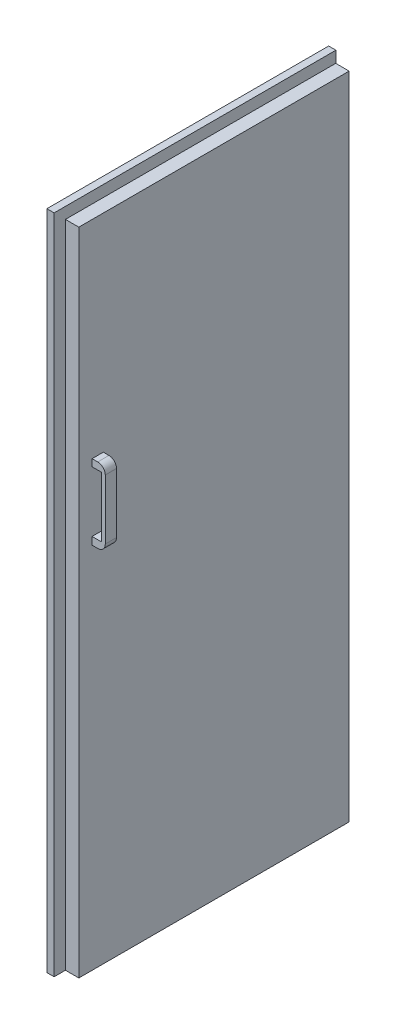
SolidWorks part; units mm, degrees
ref_plane "Front Plane" through (0, 0, 0) normal (0, 0, 1) x (1, 0, 0)
ref_plane "Top Plane" through (0, 0, 0) normal (0, 1, 0) x (1, 0, 0)
ref_plane "Right Plane" through (0, 0, 0) normal (1, 0, 0) x (0, 0, -1)
sketch "Sketch1" plane through (0, 0, 0) normal (0, 1, 0) x (1, 0, 0)
  line L1 (0, 0) -> (54.7584, 0)
  line L2 (0, 0) -> (0, -717)
  line L3 (0, -717) -> (54.7584, -717)
  line L4 (54.7584, 0) -> (54.7584, -717)
extrude "Boss-Extrude1" add sketch "Sketch1" along normal blind 1725
sketch "Sketch2" plane through (0, 0, 717) normal (0, 0, 1) x (1, 0, 0)
  line L0 (0, 0) -> (54.7584, 0) construction
  line L1 (0, 1725) -> (19.2176, 1725)
  line L2 (0, 1725) -> (0, 0)
  line L3 (0, 0) -> (19.2176, 0)
  line L4 (19.2176, 1725) -> (19.2176, 0)
extrude "Boss-Extrude2" add sketch "Sketch2" along normal blind 30
sketch "Sketch3" plane through (0, 1725, 0) normal (0, 1, 0) x (1, 0, 0)
  line L1 (19.2176, -747) -> (0, -747)
  line L2 (19.2176, -747) -> (19.2176, 0.4709)
  line L3 (19.2176, 0.4709) -> (0, 0.4709)
  line L4 (0, -747) -> (0, 0.4709)
extrude "Boss-Extrude3" add sketch "Sketch3" along normal blind 30 contours L3 L4 L1 L2
sketch "Sketch5" plane through (0, 0, 0) normal (-1, 0, 0) x (0, 0, 1)
  line L1 (0, 1745.4) -> (704.1823, 1745.4)
  line L2 (0, 1745.4) -> (0, 47.9743)
  line L3 (0, 47.9743) -> (704.1823, 47.9743)
  line L4 (704.1823, 1745.4) -> (704.1823, 47.9743)
extrude "Cut-Extrude1" cut sketch "Sketch5" against normal blind 8.6053
sketch "Sketch6" plane through (8.6053, 0, 0) normal (-1, 0, 0) x (0, 0, 1)
  line L0 (0, 1745.4) -> (0, 1725) construction
  line L1 (0, 991.273) -> (704.1823, 991.273)
  line L2 (0, 991.273) -> (0, 947.3587)
  line L3 (0, 947.3587) -> (704.1823, 947.3587)
  line L4 (704.1823, 991.273) -> (704.1823, 947.3587)
  line L5 (704.1823, 47.9743) -> (704.1823, 1745.4) construction
extrude "Boss-Extrude5" add sketch "Sketch6" along normal blind 9
sketch "Sketch7" plane through (8.6053, 0, 0) normal (-1, 0, 0) x (0, 0, 1)
  line L1 (632.6204, 1093.6547) -> (662.5353, 1093.6547)
  line L2 (632.6204, 1093.6547) -> (632.6204, 1073.0238)
  line L3 (632.6204, 1073.0238) -> (662.5353, 1073.0238)
  line L4 (662.5353, 1093.6547) -> (662.5353, 1073.0238)
extrude "Boss-Extrude6" add sketch "Sketch7" along normal blind 35
sketch "Sketch8" plane through (8.6053, 0, 0) normal (-1, 0, 0) x (0, 0, 1)
  line L1 (630.0415, 883.2191) -> (659.9564, 883.2191)
  line L2 (630.0415, 883.2191) -> (630.0415, 862.5881)
  line L3 (630.0415, 862.5881) -> (659.9564, 862.5881)
  line L4 (659.9564, 883.2191) -> (659.9564, 862.5881)
extrude "Boss-Extrude7" add sketch "Sketch8" along normal blind 35
sketch "Sketch9" plane through (-26.3947, 0, 0) normal (-1, 0, 0) x (0, 0, 1)
  line L1 (632.6204, 1093.6547) -> (659.9564, 1093.6547)
  line L2 (632.6204, 1093.6547) -> (632.6204, 862.5881)
  line L3 (632.6204, 862.5881) -> (659.9564, 862.5881)
  line L4 (659.9564, 1093.6547) -> (659.9564, 862.5881)
extrude "Boss-Extrude8" add sketch "Sketch9" along normal blind 10
sketch "Sketch10" plane through (-26.3947, 0, 0) normal (-1, 0, 0) x (0, 0, 1)
  line L1 (659.9564, 1093.6547) -> (662.5353, 1093.6547)
  line L2 (659.9564, 1093.6547) -> (659.9564, 1073.0238)
  line L3 (659.9564, 1073.0238) -> (662.5353, 1073.0238)
  line L4 (662.5353, 1093.6547) -> (662.5353, 1073.0238)
extrude "Cut-Extrude2" cut sketch "Sketch10" against normal blind 35
sketch "Sketch11" plane through (-26.3947, 0, 0) normal (-1, 0, 0) x (0, 0, 1)
  line L1 (630.0415, 883.2191) -> (632.6204, 883.2191)
  line L2 (630.0415, 883.2191) -> (630.0415, 862.5881)
  line L3 (630.0415, 862.5881) -> (632.6204, 862.5881)
  line L4 (632.6204, 883.2191) -> (632.6204, 862.5881)
extrude "Cut-Extrude3" cut sketch "Sketch11" against normal blind 35
fillet "Fillet2" radius 20 1 edges at (-36.3947, 862.5881, 646.2884)
fillet "Fillet3" radius 20 1 edges at (-36.3947, 1093.6547, 646.2884)
sketch "Sketch12" plane through (54.7584, 0, 0) normal (1, 0, 0) x (0, 0, -1)
  line L1 (-681.883, 1175.5139) -> (-652.1154, 1175.5139)
  line L2 (-681.883, 1175.5139) -> (-681.883, 1156.8226)
  line L3 (-681.883, 1156.8226) -> (-652.1154, 1156.8226)
  line L4 (-652.1154, 1175.5139) -> (-652.1154, 1156.8226)
  line L5 (-681.883, 996.9086) -> (-652.1154, 996.9086)
  line L6 (-681.883, 996.9086) -> (-681.883, 976.8329)
  line L7 (-681.883, 976.8329) -> (-652.1154, 976.8329)
  line L8 (-652.1154, 996.9086) -> (-652.1154, 976.8329)
extrude "Boss-Extrude9" add sketch "Sketch12" along normal blind 25
sketch "Sketch13" plane through (79.7584, 0, 0) normal (1, 0, 0) x (0, 0, -1)
  line L1 (-681.883, 1175.5139) -> (-652.1154, 1175.5139)
  line L2 (-681.883, 1175.5139) -> (-681.883, 976.8329)
  line L3 (-681.883, 976.8329) -> (-652.1154, 976.8329)
  line L4 (-652.1154, 1175.5139) -> (-652.1154, 976.8329)
extrude "Boss-Extrude10" add sketch "Sketch13" along normal blind 10
fillet "Fillet4" radius 20 1 edges at (89.7584, 1175.5139, 666.9992)
fillet "Fillet5" radius 20 1 edges at (89.7584, 976.8329, 666.9992)
